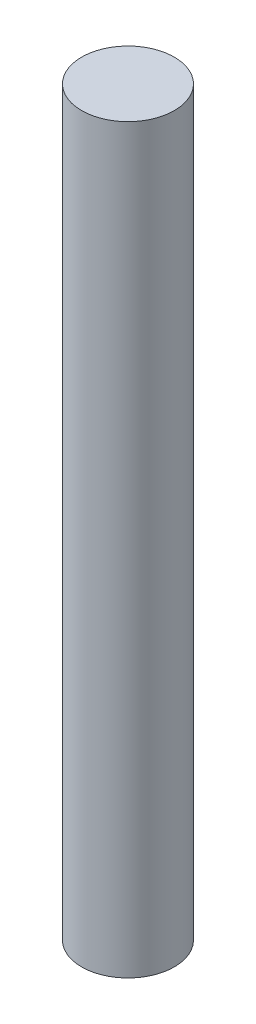
SolidWorks part; units mm, degrees
ref_plane "Front Plane" through (0, 0, 0) normal (0, 0, 1) x (1, 0, 0)
ref_plane "Top Plane" through (0, 0, 0) normal (0, 1, 0) x (1, 0, 0)
ref_plane "Right Plane" through (0, 0, 0) normal (1, 0, 0) x (0, 0, -1)
sketch "Sketch1" plane through (0, 0, 0) normal (0, 1, 0) x (1, 0, 0)
  circle A0 centre (0, 0) radius 3.175
  dimension "D1" = 6.35
extrude "Boss-Extrude1" add sketch "Sketch1" along normal blind 50.8 contours A0
equation "\"initial\"=2"
equation "\"initial_height\"= 2.5"
